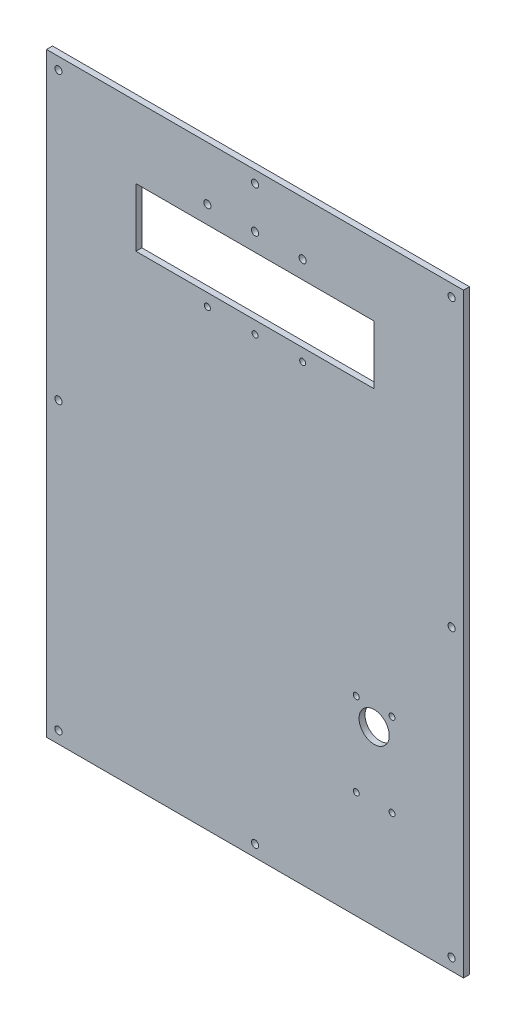
SolidWorks part; units mm, degrees
material "ABS"
ref_plane "Front Plane" through (0, 0, 0) normal (0, 0, 1) x (1, 0, 0)
ref_plane "Top Plane" through (0, 0, 0) normal (0, 1, 0) x (1, 0, 0)
ref_plane "Right Plane" through (0, 0, 0) normal (1, 0, 0) x (0, 0, -1)
sketch "Sketch1" plane through (0, 0, 0) normal (0, 0, 1) x (1, 0, 0)
  line L0 (0, 250) -> (0, -250) construction
  line L1 (-175, -250) -> (175, -250)
  line L2 (-175, -250) -> (-175, 250)
  line L3 (-175, 250) -> (175, 250)
  line L4 (175, -250) -> (175, 250)
  line L5 (-175, -250) -> (175, 250) construction
  line L6 (-175, 250) -> (175, -250) construction
  line L7 (-165, 250) -> (-165, -250) construction
  line L8 (175, 205) -> (-175, 205) construction
  line L9 (100, 190) -> (-100, 190)
  line L10 (100, 190) -> (100, 140.8)
  line L11 (100, 140.8) -> (-100, 140.8)
  line L12 (-100, 190) -> (-100, 140.8)
  line L13 (100, 190) -> (-100, 140.8) construction
  line L14 (100, 140.8) -> (-100, 190) construction
  line L15 (-175, 130.4) -> (175, 130.4) construction
  line L17 (115, -90) -> (85, -90) construction
  line L18 (115, -90) -> (115, -160) construction
  line L19 (115, -160) -> (85, -160) construction
  line L20 (85, -90) -> (85, -160) construction
  line L21 (115, -90) -> (85, -160) construction
  line L22 (115, -160) -> (85, -90) construction
  circle A2 centre (-165, 0) radius 3
  circle A3 centre (165, -240) radius 3
  circle A4 centre (165, 0) radius 3
  circle A5 centre (165, 240) radius 3
  circle A6 centre (0, 240) radius 3
  circle A7 centre (0, -240) radius 3
  circle A8 centre (-165, 240) radius 3
  circle A9 centre (-165, -240) radius 3
  circle A10 centre (40, 205) radius 3
  circle A11 centre (0, 205) radius 3
  circle A12 centre (-40, 205) radius 3
  circle A13 centre (0, 130.4) radius 2.5
  circle A14 centre (40, 130.4) radius 2.5
  circle A15 centre (-40, 130.4) radius 2.5
  circle A16 centre (115, -90) radius 2.5
  circle A17 centre (85, -90) radius 2.5
  circle A18 centre (115, -160) radius 2.5
  circle A19 centre (85, -160) radius 2.5
  circle A20 centre (100, -105) radius 12.665
  point P0 (0, 0)
  point P27 (0, 165.4)
  point P47 (100, -125)
  dimension "D4" = 6
  dimension "D6" = 10
  dimension "D8" = 6
  dimension "D18" = 6
  dimension "D21" = 5
  dimension "D25" = 5
  dimension "D28" = 25.33
  dimension "D1" = 350
  dimension "D2" = 500
  dimension "D3" = 10
  dimension "D5" = 10
  dimension "D7" = 10
  dimension "D9" = 10
  dimension "D10" = 10
  dimension "D11" = 10
  dimension "D12" = 10
  dimension "D13" = 10
  dimension "D14" = 200
  dimension "D15" = 49.2
  dimension "D16" = 60
  dimension "D17" = 15
  dimension "D19" = 60
  dimension "D20" = 10.4
  dimension "D22" = 40
  dimension "D23" = 70
  dimension "D24" = 30
  dimension "D26" = 60
  dimension "D27" = 90
  dimension "D29" = 15
extrude "Boss-Extrude1" add sketch "Sketch1" along normal blind 5
